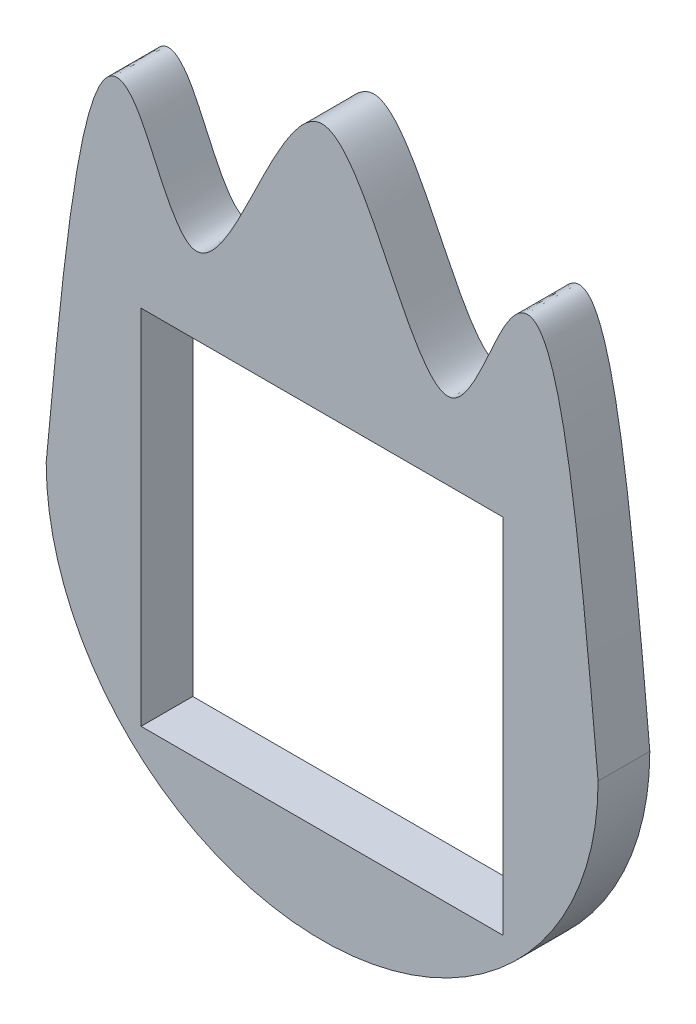
SolidWorks part; units mm, degrees
ref_plane "Front Plane" through (0, 0, 0) normal (0, 0, 1) x (1, 0, 0)
ref_plane "Top Plane" through (0, 0, 0) normal (0, 1, 0) x (1, 0, 0)
ref_plane "Right Plane" through (0, 0, 0) normal (1, 0, 0) x (0, 0, -1)
sketch "Model" plane through (0, 0, 0) normal (0, 0, 1) x (1, 0, 0)
  line L0 (25.0162, 60.9246) -> (67.0162, 60.9246)
  line L1 (67.0162, 60.9246) -> (67.0162, 18.9246)
  line L2 (67.0162, 18.9246) -> (25.0162, 18.9246)
  line L3 (25.0162, 18.9246) -> (25.0162, 60.9246)
  arc A0 (14.0162, 39.9246) -> (78.0162, 39.9246) centre (46.0162, 39.9246) ccw
  spline S0 degree 3 poles (14.0162, 39.9246) (16.4205, 65.6132) (19.5007, 98.5232) (30.9828, 64.0313) (38.5679, 80.286) (46.0162, 94.7439) (53.4645, 80.286) (61.0497, 64.0313) (72.5317, 98.5232) (75.6119, 65.6132) (78.0162, 39.9246) knots 0 0 0 0 0.265429 0.340045 0.420022 0.5 0.579978 0.659955 0.734571 1 1 1 1
extrude "Boss-Extrude1" add sketch "Model" along normal blind 6 contours L3 L2 L1 L0 | S0 A0
